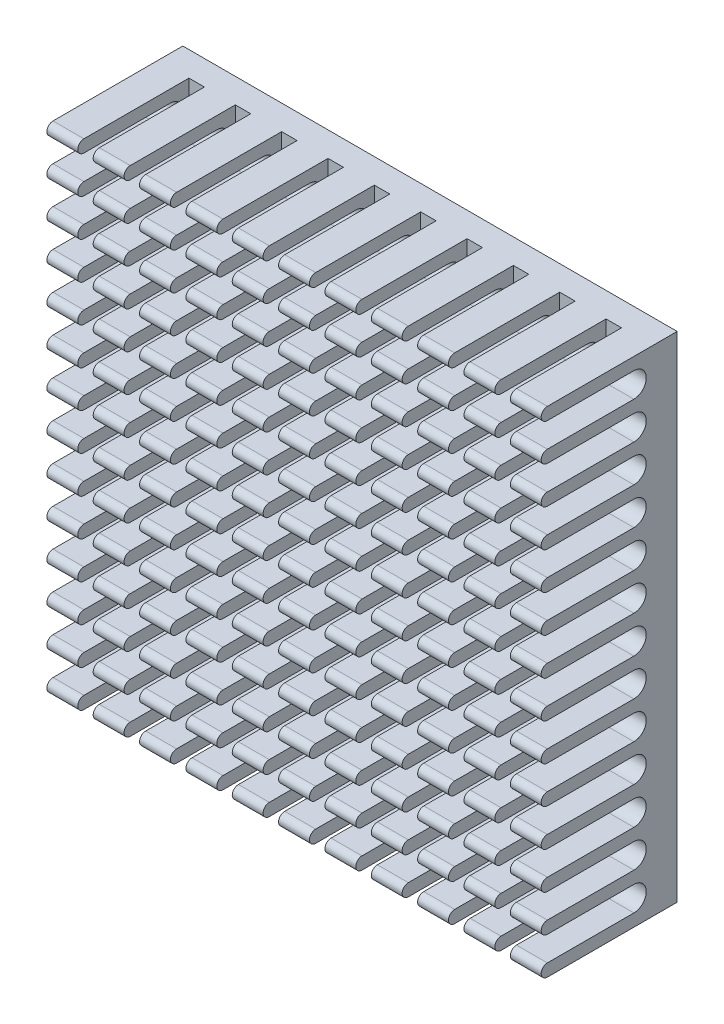
SolidWorks part; units mm, degrees
ref_plane "Front Plane" through (0, 0, 0) normal (1, 0, 0) x (0, 1, 0)
ref_plane "Top Plane" through (0, 0, 0) normal (0, 0, 1) x (0, 1, 0)
ref_plane "Right Plane" through (0, 0, 0) normal (0, 1, 0) x (-1, 0, 0)
sketch "Sketch1" plane through (0, 0, 0) normal (0, 0, 1) x (0, 1, 0)
  line L1 (-20, 20) -> (20, 20)
  line L2 (-20, 20) -> (-20, -20)
  line L3 (-20, -20) -> (20, -20)
  line L4 (20, 20) -> (20, -20)
  line L5 (-20, 20) -> (20, -20) construction
  line L6 (-20, -20) -> (20, 20) construction
  point P0 (0, 0)
  dimension "D1" = 40
  dimension "D2" = 40
extrude "Boss-Extrude1" add sketch "Sketch1" along normal blind 11
sketch "Sketch2" plane through (0, 0, 0) normal (1, 0, 0) x (0, 1, 0)
  line L1 (-20, 11) -> (-20, 0) construction
  line L2 (-20, 11) -> (20, 11) construction
  line L3 (-19, 10.5) -> (-19, 3.5)
  line L4 (-17, 3.5) -> (-17, 10.5)
  line L5 (-16, 10.5) -> (-16, 3.5)
  line L6 (-14, 3.5) -> (-14, 10.5)
  line L7 (-13, 10.5) -> (-13, 3.5)
  line L8 (-11, 3.5) -> (-11, 10.5)
  line L9 (-10, 10.5) -> (-10, 3.5)
  line L10 (-8, 3.5) -> (-8, 10.5)
  line L11 (-7, 10.5) -> (-7, 3.5)
  line L12 (-5, 3.5) -> (-5, 10.5)
  line L13 (-4, 10.5) -> (-4, 3.5)
  line L14 (-2, 3.5) -> (-2, 10.5)
  line L15 (-1, 10.5) -> (-1, 3.5)
  line L16 (1, 3.5) -> (1, 10.5)
  line L17 (2, 10.5) -> (2, 3.5)
  line L18 (4, 3.5) -> (4, 10.5)
  line L19 (5, 10.5) -> (5, 3.5)
  line L20 (7, 3.5) -> (7, 10.5)
  line L21 (8, 10.5) -> (8, 3.5)
  line L22 (10, 3.5) -> (10, 10.5)
  line L23 (11, 10.5) -> (11, 3.5)
  line L24 (13, 3.5) -> (13, 10.5)
  line L25 (14, 10.5) -> (14, 3.5)
  line L26 (16, 3.5) -> (16, 10.5)
  line L27 (17, 10.5) -> (17, 3.5)
  line L28 (19, 3.5) -> (19, 10.5)
  line L30 (-20, 10.5) -> (-20, 11)
  line L31 (-20, 11) -> (20, 11)
  line L32 (20, 11) -> (20, 10.5)
  line L34 (20, 10.5) -> (20, 3.5)
  arc A0 (-20, 10.5) -> (-19, 10.5) centre (-19.5, 10.5) cw
  arc A1 (-19, 3.5) -> (-17, 3.5) centre (-18, 3.5) ccw
  arc A2 (-17, 10.5) -> (-16, 10.5) centre (-16.5, 10.5) cw
  arc A3 (-16, 3.5) -> (-14, 3.5) centre (-15, 3.5) ccw
  arc A4 (-14, 10.5) -> (-13, 10.5) centre (-13.5, 10.5) cw
  arc A5 (-13, 3.5) -> (-11, 3.5) centre (-12, 3.5) ccw
  arc A6 (-11, 10.5) -> (-10, 10.5) centre (-10.5, 10.5) cw
  arc A7 (-10, 3.5) -> (-8, 3.5) centre (-9, 3.5) ccw
  arc A8 (-8, 10.5) -> (-7, 10.5) centre (-7.5, 10.5) cw
  arc A9 (-7, 3.5) -> (-5, 3.5) centre (-6, 3.5) ccw
  arc A10 (-5, 10.5) -> (-4, 10.5) centre (-4.5, 10.5) cw
  arc A11 (-4, 3.5) -> (-2, 3.5) centre (-3, 3.5) ccw
  arc A12 (-2, 10.5) -> (-1, 10.5) centre (-1.5, 10.5) cw
  arc A13 (-1, 3.5) -> (1, 3.5) centre (0, 3.5) ccw
  arc A14 (1, 10.5) -> (2, 10.5) centre (1.5, 10.5) cw
  arc A15 (2, 3.5) -> (4, 3.5) centre (3, 3.5) ccw
  arc A16 (4, 10.5) -> (5, 10.5) centre (4.5, 10.5) cw
  arc A17 (5, 3.5) -> (7, 3.5) centre (6, 3.5) ccw
  arc A18 (7, 10.5) -> (8, 10.5) centre (7.5, 10.5) cw
  arc A19 (8, 3.5) -> (10, 3.5) centre (9, 3.5) ccw
  arc A20 (10, 10.5) -> (11, 10.5) centre (10.5, 10.5) cw
  arc A21 (11, 3.5) -> (13, 3.5) centre (12, 3.5) ccw
  arc A22 (13, 10.5) -> (14, 10.5) centre (13.5, 10.5) cw
  arc A23 (14, 3.5) -> (16, 3.5) centre (15, 3.5) ccw
  arc A24 (16, 10.5) -> (17, 10.5) centre (16.5, 10.5) cw
  arc A25 (17, 3.5) -> (19, 3.5) centre (18, 3.5) ccw
  arc A26 (19, 10.5) -> (20, 10.5) centre (19.5, 10.5) cw
  arc A28 (20, 3.5) -> (22, 3.5) centre (21, 3.5) ccw
  point P11 (-18, 2.5)
  point P12 (-19.5, 11)
  dimension "D1" = 2
  dimension "D2" = 0.5
  dimension "D3" = 8.5
  dimension "D4" = 14
extrude "Cut-Extrude1" cut sketch "Sketch2" against normal through all and the other way through all contours L4 A2 L31 A0 L3 A1 | L6 A4 L31 A2 L5 A3 | L8 A6 L31 A4 L7 A5 | L30 A0 L31 | L10 A8 L31 A6 L9 A7 | L12 A10 L31 A8 L11 A9 | L14 A12 L31 A10 L13 A11 | L16 A14 L31 A12 L15 A13 | L18 A16 L31 A14 L17 A15 | L20 A18 L31 A16 L19 A17 | L22 A20 L31 A18 L21 A19 | L24 A22 L31 A20 L23 A21 | L26 A24 L31 A22 L25 A23 | L28 A26 L31 A24 L27 A25 | L31 A26 L32
sketch "Sketch3" plane through (0, 0, 0) normal (0, 1, 0) x (-1, 0, 0)
  line L0 (-17.5, 11) -> (-17.5, 2)
  line L1 (20, 11) -> (-20, 11) construction
  line L2 (-17.5, 2) -> (-16.25, 2)
  line L3 (-16.25, 2) -> (-16.25, 11)
  line L4 (-20, 10.5) -> (-20, 0) construction
  line L5 (-16.25, 11) -> (-17.5, 11)
  line L6 (-12.5, 11) -> (-13.75, 11)
  line L7 (-13.75, 11) -> (-13.75, 2)
  line L8 (-13.75, 2) -> (-12.5, 2)
  line L9 (-12.5, 2) -> (-12.5, 11)
  line L10 (-8.75, 11) -> (-10, 11)
  line L11 (-10, 11) -> (-10, 2)
  line L12 (-10, 2) -> (-8.75, 2)
  line L13 (-8.75, 2) -> (-8.75, 11)
  line L14 (-5, 11) -> (-6.25, 11)
  line L15 (-6.25, 11) -> (-6.25, 2)
  line L16 (-6.25, 2) -> (-5, 2)
  line L17 (-5, 2) -> (-5, 11)
  line L18 (-1.25, 11) -> (-2.5, 11)
  line L19 (-2.5, 11) -> (-2.5, 2)
  line L20 (-2.5, 2) -> (-1.25, 2)
  line L21 (-1.25, 2) -> (-1.25, 11)
  line L22 (2.5, 11) -> (1.25, 11)
  line L23 (1.25, 11) -> (1.25, 2)
  line L24 (1.25, 2) -> (2.5, 2)
  line L25 (2.5, 2) -> (2.5, 11)
  line L26 (6.25, 11) -> (5, 11)
  line L27 (5, 11) -> (5, 2)
  line L28 (5, 2) -> (6.25, 2)
  line L29 (6.25, 2) -> (6.25, 11)
  line L30 (10, 11) -> (8.75, 11)
  line L31 (8.75, 11) -> (8.75, 2)
  line L32 (8.75, 2) -> (10, 2)
  line L33 (10, 2) -> (10, 11)
  line L34 (13.75, 11) -> (12.5, 11)
  line L35 (12.5, 11) -> (12.5, 2)
  line L36 (12.5, 2) -> (13.75, 2)
  line L37 (13.75, 2) -> (13.75, 11)
  line L38 (17.5, 11) -> (16.25, 11)
  line L39 (16.25, 11) -> (16.25, 2)
  line L40 (16.25, 2) -> (17.5, 2)
  line L41 (17.5, 2) -> (17.5, 11)
  dimension "D1" = 10
  dimension "2.25" = 2.5
  dimension "D2" = 1.25
  dimension "D3" = 9
extrude "Cut-Extrude2" cut sketch "Sketch3" against normal through all and the other way through all
